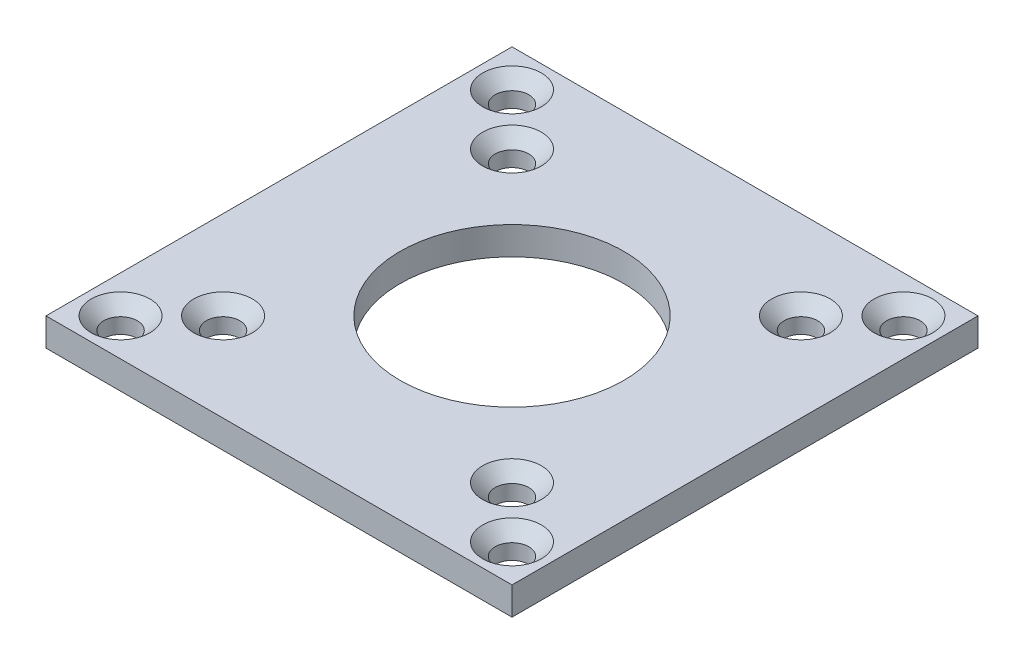
SolidWorks part; units mm, degrees
ref_plane "Front Plane" through (0, 0, 0) normal (0, 0, 1) x (1, 0, 0)
ref_plane "Top Plane" through (0, 0, 0) normal (0, 1, 0) x (1, 0, 0)
ref_plane "Right Plane" through (0, 0, 0) normal (1, 0, 0) x (0, 0, -1)
sketch "Plate" plane through (0, 0, 0) normal (0, 1, 0) x (1, 0, 0)
  line L1 (25, -25) -> (-25, -25)
  line L2 (25, -25) -> (25, 25)
  line L3 (25, 25) -> (-25, 25)
  line L4 (-25, -25) -> (-25, 25)
  line L5 (25, -25) -> (-25, 25) construction
  line L6 (25, 25) -> (-25, -25) construction
  point P0 (0, 0)
  dimension "D1" = 50
  dimension "D2" = 50
extrude "Boss-Extrude1" add sketch "Plate" along normal blind 3
hole_wizard "CSK for M3 Oval Head Machine Screw1" positions "3DSketch3" profile "Sketch3" countersink size "M3" standard "ANSI Metric" end condition through all
sketch3d "3DSketch3"
  line L0 (-25, 3, -25) -> (-25, 3, 25) construction
  line L1 (-25, 3, 25) -> (25, 3, 25) construction
  line L2 (25, 3, -25) -> (-25, 3, -25) construction
  line L3 (25, 3, 25) -> (25, 3, -25) construction
  point P0 (-21, 3, 21)
  point P2 (-21, 3, -21)
  point P4 (21, 3, -21)
  point P6 (21, 3, 21)
  dimension "D1" = 4
  dimension "D2" = 4
  dimension "D3" = 4
  dimension "D4" = 4
  dimension "D5" = 4
  dimension "D6" = 4
  dimension "D7" = 4
  dimension "D8" = 4
sketch "Sketch3" plane through (-21, 3, 21) normal (1, 0, 0) x (0, 0, 1)
  line L0 (0, 0) -> (0, 3)
  line L1 (0, 3) -> (1.8, 3)
  line L2 (1.8, 3) -> (1.8, 1.35)
  line L3 (1.8, 1.35) -> (3.15, 0)
  line L5 (3.15, 0) -> (0, 0)
  line L6 (-1.8, 1.35) -> (-3.15, 0) construction
  line L11 (0, -6.35) -> (0, 107.95) construction
  dimension "Thru Hole Dia." = 3.6
  dimension "Thru Hole Depth" = 3
  dimension "Near C'Sink Dia." = 6.3
  dimension "Near C'Sink Angle" = 90
hole_wizard "Ø24.0 (24) Diameter Hole1" positions "3DSketch4" profile "Sketch4" hole size "Ø24.0" standard "ANSI Metric" end condition through all
sketch3d "3DSketch4"
  line L0 (-25, 3, -25) -> (-25, 3, 25) construction
  line L1 (-25, 3, 25) -> (25, 3, 25) construction
  point P0 (0, 0, 0)
  point P3 (0, 0, 0)
  point P5 (0, 0, 0)
  point P7 (0, 0, 0)
  point P9 (0, 0, 0)
  point P11 (0, 0, 0)
  point P13 (0, 3, 0)
  point P20 (-62.0611, -166.0487, 0)
  dimension "D1" = 25
  dimension "D2" = 25
sketch "Sketch4" plane through (0, 3, 0) normal (1, 0, 0) x (0, 0, 1)
  line L0 (0, 0) -> (0, 3)
  line L1 (0, 3) -> (12, 3)
  line L2 (12, 3) -> (12, 0)
  line L5 (12, 0) -> (0, 0)
  line L11 (0, -6.35) -> (0, 107.95) construction
  dimension "Thru Hole Dia." = 24
  dimension "Thru Hole Depth" = 3
hole_wizard "CSK for M3 Oval Head Machine Screw2" positions "Sketch5" profile "Sketch6" countersink size "M3" standard "ANSI Metric" end condition through all
sketch "Sketch5" plane through (0, 3, 0) normal (0, 1, 0) x (1, 0, 0)
  point P0 (-15.5, 15.5)
  point P3 (15.5, 15.5)
  point P6 (15.5, -15.5)
  point P9 (-15.5, -15.5)
sketch "Sketch6" plane through (-15.5, 3, -15.5) normal (1, 0, 0) x (0, 0, 1)
  line L0 (0, 0) -> (0, 3)
  line L1 (0, 3) -> (1.8, 3)
  line L2 (1.8, 3) -> (1.8, 1.35)
  line L3 (1.8, 1.35) -> (3.15, 0)
  line L5 (3.15, 0) -> (0, 0)
  line L6 (-1.8, 1.35) -> (-3.15, 0) construction
  line L11 (0, -6.35) -> (0, 107.95) construction
  dimension "Thru Hole Dia." = 3.6
  dimension "Thru Hole Depth" = 3
  dimension "Near C'Sink Dia." = 6.3
  dimension "Near C'Sink Angle" = 90
